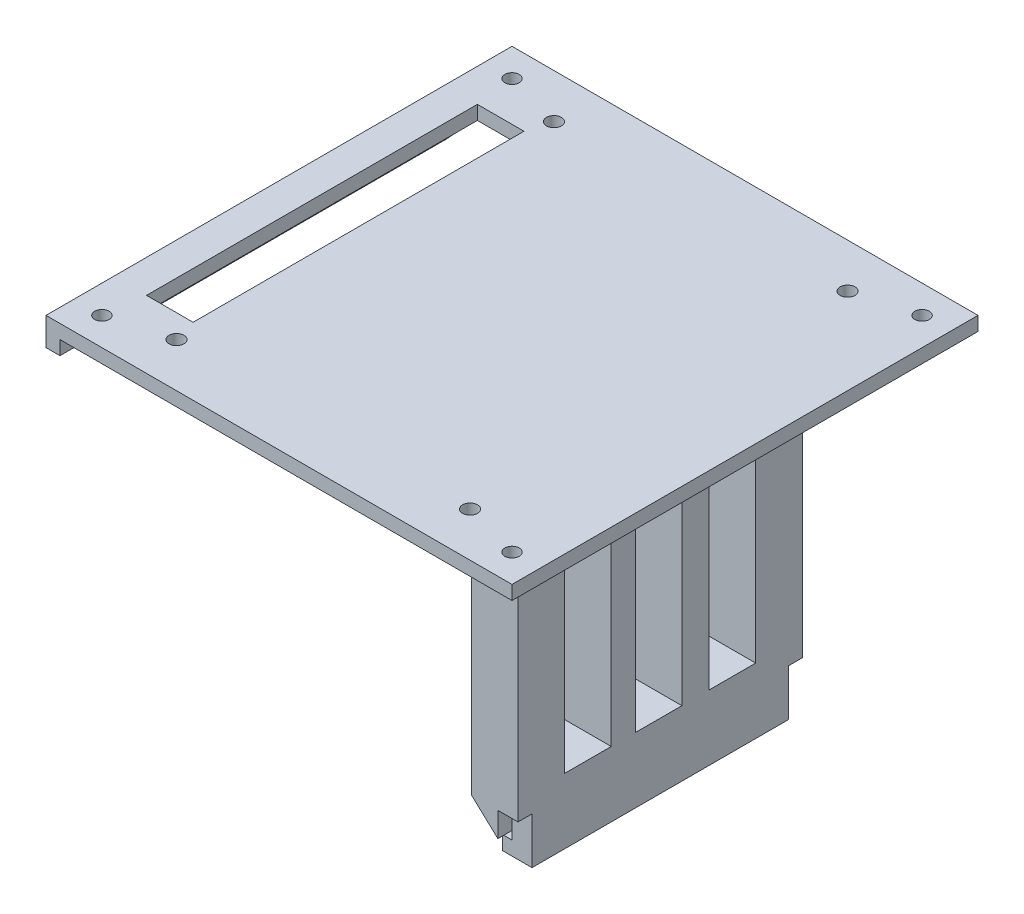
SolidWorks part; units mm, degrees
ref_plane "Front" through (0, 0, 0) normal (0, 0, 1) x (1, 0, 0)
ref_plane "Top" through (0, 0, 0) normal (0, 1, 0) x (1, 0, 0)
ref_plane "Right" through (0, 0, 0) normal (1, 0, 0) x (0, 0, -1)
sketch "Croquis1" plane through (0, 0, 0) normal (0, 1, 0) x (1, 0, 0)
  line L1 (-50, 50) -> (50, 50)
  line L2 (-50, 50) -> (-50, -50)
  line L3 (-50, -50) -> (50, -50)
  line L4 (50, 50) -> (50, -50)
  dimension "D1" = 50
  dimension "D2" = 50
  dimension "D3" = 50
  dimension "D4" = 50
extrude "Saliente-Extruir1" add sketch "Croquis1" along normal blind 3
sketch "Croquis6" plane through (0, 3, 0) normal (0, 1, 0) x (1, 0, 0)
  line L0 (50, 50) -> (-50, 50) construction
  line L1 (-50, 50) -> (-50, -50) construction
  line L2 (50, -50) -> (50, 50) construction
  line L3 (-50, -50) -> (50, -50) construction
  circle A0 centre (-44, 44) radius 1.55
  circle A1 centre (44, 44) radius 1.55
  circle A2 centre (44, -44) radius 1.55
  circle A3 centre (-44, -44) radius 1.55
  dimension "D1" = 3.1
  dimension "D5" = 3.1
  dimension "D9" = 3.1
  dimension "D12" = 3.1
  dimension "D2" = 6
  dimension "D3" = 6
  dimension "D4" = 6
  dimension "D6" = 6
  dimension "D7" = 6
  dimension "D8" = 6
  dimension "D10" = 6
  dimension "D11" = 6
extrude "Cortar-Extruir4" cut sketch "Croquis6" against normal blind 10
sketch "Croquis7" plane through (0, 3, 0) normal (0, 1, 0) x (1, 0, 0)
  line L0 (-50, 50) -> (-50, -50) construction
  line L2 (50, -50) -> (50, 50) construction
  line L3 (50, 50) -> (-50, 50) construction
  line L5 (-50, -50) -> (50, -50) construction
  circle A0 centre (-31.5, 40.5) radius 1.6
  circle A1 centre (31.5, 40.5) radius 1.6
  circle A2 centre (-31.5, -40.5) radius 1.6
  circle A3 centre (31.5, -40.5) radius 1.6
  dimension "D1" = 63
  dimension "D5" = 3.2
  dimension "D6" = 3.2
  dimension "D7" = 3.2
  dimension "D8" = 3.2
  dimension "D2" = 63
  dimension "D3" = 81
  dimension "D4" = 81
  dimension "D9" = 18.5
  dimension "D10" = 18.5
  dimension "D11" = 9.5
  dimension "D12" = 9.5
  dimension "D13" = 9.5
  dimension "D14" = 9.5
extrude "Cortar-Extruir5" cut sketch "Croquis7" against normal blind 10
sketch "Croquis8" plane through (0, 0, 0) normal (0, -1, 0) x (1, 0, 0)
  line L0 (50, -50) -> (-50, -50) construction
  line L1 (-50, 50) -> (-47, 50)
  line L2 (-50, 50) -> (-50, -50)
  line L3 (-50, -50) -> (-47, -50)
  line L4 (-47, 50) -> (-47, -50)
  dimension "D1" = 3
extrude "Saliente-Extruir3" add sketch "Croquis8" along normal blind 3
sketch "Croquis9" plane through (0, 0, 0) normal (0, -1, 0) x (1, 0, 0)
  line L1 (21.7935, 30.5) -> (31.7935, 30.5)
  line L2 (21.7935, 30.5) -> (21.7935, -30.5)
  line L3 (21.7935, -30.5) -> (31.7935, -30.5)
  line L4 (31.7935, 30.5) -> (31.7935, -30.5)
  circle A0 centre (31.5, 40.5) radius 1.6 construction
  circle A1 centre (31.5, -40.5) radius 1.6 construction
  dimension "D2" = 10
  dimension "D1" = 10
  dimension "D3" = 10
extrude "Saliente-Extruir4" add sketch "Croquis9" along normal blind 60
sketch "Croquis10" plane through (0, -60, 0) normal (0, -1, 0) x (1, 0, 0)
  line L0 (27.4717, 85.6822) -> (27.4717, -78.3178) construction
  line L1 (27.4717, 27.5) -> (31.7935, 27.5)
  line L2 (27.4717, 27.5) -> (27.4717, -27.5)
  line L3 (27.4717, -27.5) -> (31.7935, -27.5)
  line L4 (31.7935, 27.5) -> (31.7935, -27.5)
  line L5 (31.7935, -30.5) -> (31.7935, 30.5) construction
  line L6 (31.7935, 30.5) -> (21.7935, 30.5) construction
  line L7 (21.7935, -30.5) -> (31.7935, -30.5) construction
  dimension "D1" = 3
  dimension "D2" = 3
extrude "Saliente-Extruir5" add sketch "Croquis10" along normal blind 10
sketch "Croquis11" plane through (27.4717, 0, 0) normal (-1, 0, 0) x (0, 0, 1)
  line L0 (27.5, -70) -> (27.5, -60) construction
  line L1 (-27.5, -70) -> (27.5, -70)
  line L2 (-27.5, -70) -> (-27.5, -67)
  line L3 (-27.5, -67) -> (27.5, -67)
  line L4 (27.5, -70) -> (27.5, -67)
  dimension "D1" = 3
extrude "Saliente-Extruir6" add sketch "Croquis11" along normal blind 2
sketch "Croquis12" plane through (0, 0, 30.5) normal (0, 0, 1) x (1, 0, 0)
  line L0 (21.7935, -60) -> (27.4717, -60)
  line L1 (27.4717, -60) -> (27.4717, -65.2636)
  line L2 (27.4717, -67) -> (27.4717, -60) construction
  line L3 (-42.9319, 0) -> (27.4717, -65.2636) construction
  line L4 (27.4717, -65.2636) -> (21.7935, -60)
  line L5 (-44.6994, -1.9068) -> (-47, -1.9068)
  line L6 (-47, -3) -> (-47, 0) construction
  line L7 (-47, -1.9068) -> (-47, 0)
  line L8 (-47, 0) -> (-42.9319, 0)
  line L9 (-47, 0) -> (50, 0) construction
  line L10 (-42.9319, 0) -> (-44.6994, -1.9068) construction
  line L11 (-42.9319, 0) -> (-44.6994, -1.9068)
extrude "Saliente-Extruir7" add sketch "Croquis12" against normal blind 61
sketch "Croquis13" plane through (0, 0, 0) normal (0, -1, 0) x (1, 0, 0)
  line L1 (-42.9319, 35.5) -> (-32.9319, 35.5)
  line L2 (-42.9319, 35.5) -> (-42.9319, -35.5)
  line L3 (-42.9319, -35.5) -> (-32.9319, -35.5)
  line L4 (-32.9319, 35.5) -> (-32.9319, -35.5)
  circle A0 centre (-31.5, 40.5) radius 1.6 construction
  circle A1 centre (-31.5, -40.5) radius 1.6 construction
  dimension "D1" = 5
  dimension "D2" = 5
  dimension "D3" = 10
extrude "Cortar-Extruir6" cut sketch "Croquis13" against normal blind 61
sketch "Croquis14" plane through (31.7935, 0, 0) normal (1, 0, 0) x (0, 0, -1)
  line L0 (-30.5, -60) -> (-30.5, 0) construction
  line L1 (-20.5, -6.9742) -> (-10.5, -6.9742)
  line L2 (-20.5, -6.9742) -> (-20.5, -55.9742)
  line L3 (-20.5, -55.9742) -> (-10.5, -55.9742)
  line L4 (-10.5, -6.9742) -> (-10.5, -55.9742)
  line L5 (-5.3365, -6.9742) -> (4.6635, -6.9742)
  line L6 (-5.3365, -6.9742) -> (-5.3365, -55.9742)
  line L7 (-5.3365, -55.9742) -> (4.6635, -55.9742)
  line L8 (4.6635, -6.9742) -> (4.6635, -55.9742)
  line L9 (10.5, -6.9742) -> (20.5, -6.9742)
  line L10 (10.5, -6.9742) -> (10.5, -55.9742)
  line L11 (10.5, -55.9742) -> (20.5, -55.9742)
  line L12 (20.5, -6.9742) -> (20.5, -55.9742)
  line L13 (30.5, -60) -> (30.5, 0) construction
  dimension "D1" = 10
  dimension "D2" = 10
  dimension "D3" = 10
  dimension "D4" = 10
  dimension "D5" = 10
  dimension "D6" = 49
  dimension "D7" = 49
  dimension "D8" = 49
extrude "Cortar-Extruir7" cut sketch "Croquis14" against normal blind 61
